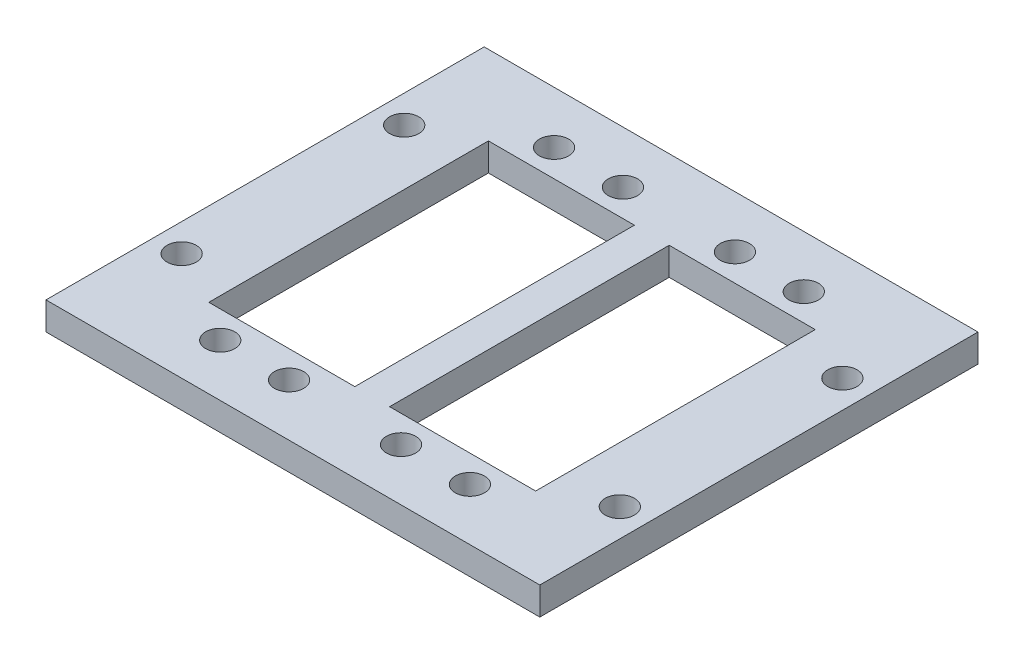
SolidWorks part; units mm, degrees
ref_plane "Front Plane" through (0, 0, 0) normal (0, 0, 1) x (1, 0, 0)
ref_plane "Top Plane" through (0, 0, 0) normal (0, 1, 0) x (1, 0, 0)
ref_plane "Right Plane" through (0, 0, 0) normal (1, 0, 0) x (0, 0, -1)
sketch "Sketch1" plane through (0, 0, 0) normal (0, 1, 0) x (1, 0, 0)
  line L4 (-97.5851, 20.3601) -> (-26.5851, 20.3601)
  line L5 (-97.5851, 20.3601) -> (-97.5851, -42.6399)
  line L6 (-97.5851, -42.6399) -> (-26.5851, -42.6399)
  line L7 (-26.5851, 20.3601) -> (-26.5851, -42.6399)
  line L8 (-62.0851, -11.1399) -> (-0.4661, -11.1399) construction
  line L9 (-85.5768, 8.9601) -> (-64.5851, 8.9601)
  line L10 (-85.5768, 8.9601) -> (-85.5768, -31.2399)
  line L11 (-85.5768, -31.2399) -> (-64.5851, -31.2399)
  line L12 (-64.5851, 8.9601) -> (-64.5851, -31.2399)
  line L13 (-59.5851, 8.9601) -> (-38.5851, 8.9601)
  line L14 (-59.5851, 8.9601) -> (-59.5851, -31.2399)
  line L15 (-59.5851, -31.2399) -> (-38.5851, -31.2399)
  line L16 (-38.5851, 8.9601) -> (-38.5851, -31.2399)
  circle A14 centre (-80.0351, 12.8601) radius 2.1
  circle A15 centre (-70.1351, 12.8601) radius 2.1
  circle A16 centre (-54.0351, 12.8601) radius 2.1
  circle A17 centre (-44.1351, 12.8601) radius 2.1
  circle A18 centre (-75.0851, -1.3399) radius 7.238
  circle A19 centre (-49.0851, -1.3399) radius 7.238
  circle A20 centre (-30.5851, 4.8601) radius 2.1
  circle A21 centre (-93.5851, 4.8601) radius 2.1
  circle A22 centre (-30.5851, -27.1399) radius 2.1
  circle A23 centre (-44.1351, -35.1399) radius 2.1
  circle A24 centre (-54.0351, -35.1399) radius 2.1
  circle A25 centre (-80.0351, -35.1399) radius 2.1
  circle A26 centre (-70.1351, -35.1399) radius 2.1
  circle A27 centre (-93.5851, -27.1399) radius 2.1
extrude "Boss-Extrude1" add sketch "Sketch1" along normal blind 4 contours L8 L5 L6 L7 L16 L15 L14 L12 L11 L10 A26 A24 A22 A23 A25 A27 | L5 L8 L10 L9 L12 L14 L13 L16 L7 L4 A14 A15 A16 A17 A20 A21
